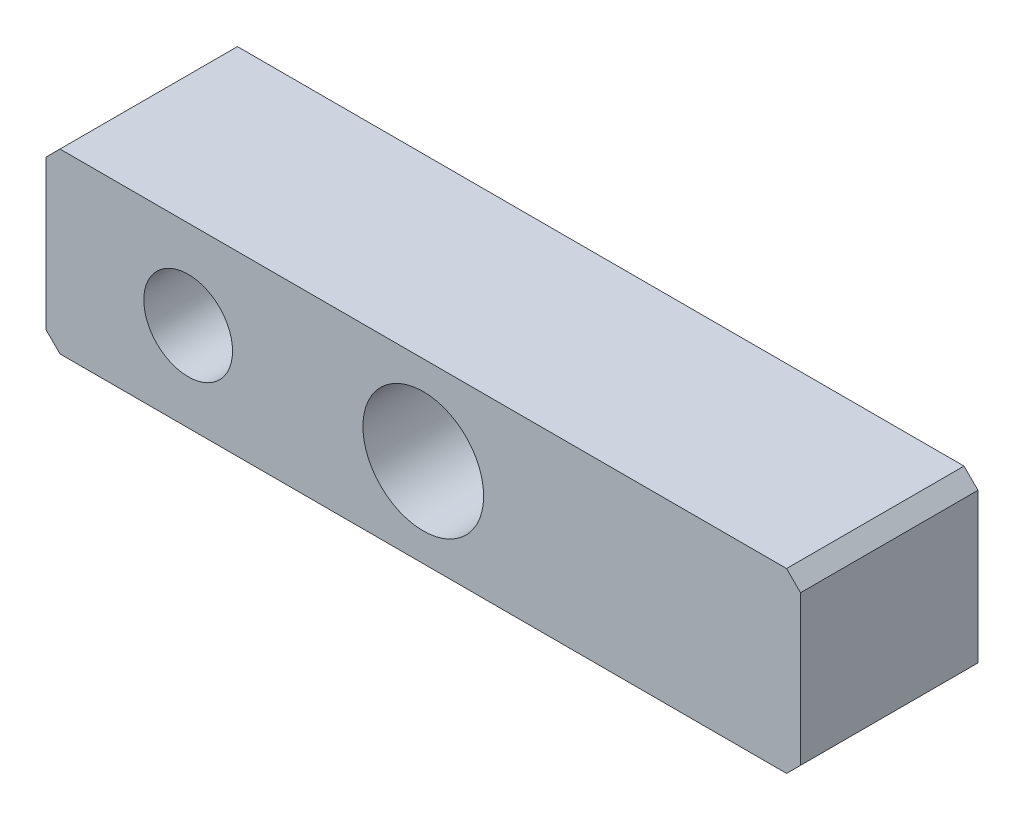
SolidWorks part; units mm, degrees
material "Balsa"
ref_plane "Front Plane" through (0, 0, 0) normal (0, 0, 1) x (1, 0, 0)
ref_plane "Top Plane" through (0, 0, 0) normal (0, 1, 0) x (1, 0, 0)
ref_plane "Right Plane" through (0, 0, 0) normal (1, 0, 0) x (0, 0, -1)
sketch "Sketch1" plane through (0, 0, 0) normal (0, 0, 1) x (1, 0, 0)
  line L0 (13.5, 0) -> (13.5, 6.35) construction
  line L1 (0, 0) -> (27, 0)
  line L2 (0, 0) -> (0, 6.35)
  line L3 (0, 6.35) -> (27, 6.35)
  line L4 (27, 0) -> (27, 6.35)
  line L5 (0, 3.175) -> (27, 3.175) construction
  circle A0 centre (13.5, 3.175) radius 2.16
  circle A1 centre (5.0875, 3.175) radius 1.5875
  dimension "D3" = 4.32
  dimension "D4" = 3.175
  dimension "D1" = 6.35
  dimension "D2" = 27
  dimension "D5" = 8.4125
extrude "Boss-Extrude1" add sketch "Sketch1" along normal blind 6.35
chamfer "Chamfer1" distance 0.5 angle 45 4 edges at (0, 0, 3.175) (0, 6.35, 3.175) (27, 6.35, 3.175) (27, 0, 3.175)
